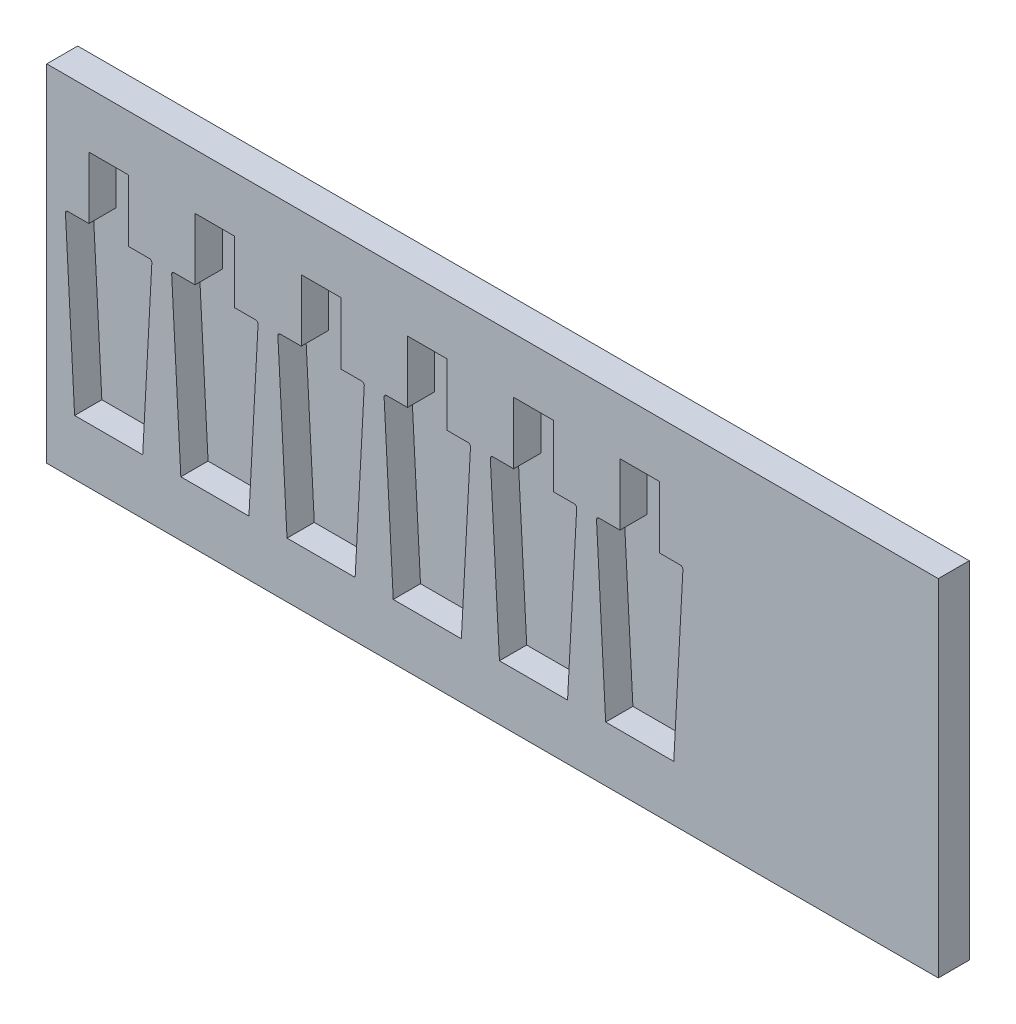
SolidWorks part; units mm, degrees
other "Markup1"
sketch "Sketch5" plane through (-360, -139.665, 25) normal (0, 0, 1) x (1, 0, 0)
ref_plane "Front Plane" through (0, 0, 0) normal (0, 0, 1) x (1, 0, 0)
ref_plane "Top Plane" through (0, 0, 0) normal (0, 1, 0) x (1, 0, 0)
ref_plane "Right Plane" through (0, 0, 0) normal (1, 0, 0) x (0, 0, -1)
sketch "Sketch2" plane through (0, 0, 0) normal (0, 0, 1) x (1, 0, 0)
  line L1 (-360, 139.665) -> (360, 139.665)
  line L2 (-360, 139.665) -> (-360, -139.665)
  line L3 (-360, -139.665) -> (360, -139.665)
  line L4 (360, 139.665) -> (360, -139.665)
  line L5 (-360, 139.665) -> (360, -139.665) construction
  line L6 (-360, -139.665) -> (360, 139.665) construction
  point P0 (0, 0)
  dimension "D1" = 720
  dimension "D2" = 279.33
extrude "Boss-Extrude1" add sketch "Sketch2" along normal blind 25
sketch "Sketch3" plane through (0, 0, 0) normal (0, 0, 1) x (1, 0, 0)
  line L0 (-326, 45) -> (-326, 95)
  line L1 (-326, 95) -> (-294, 95)
  line L2 (-294, 95) -> (-294, 45)
  line L3 (-294, 45) -> (-277.11, 45)
  line L5 (-282.5, -95) -> (-337.5, -95)
  line L7 (-342.89, 45) -> (-326, 45)
  line L9 (-344.8871, 42.893) -> (-337.5, -95)
  line L10 (-275.1129, 42.893) -> (-282.5, -95)
  line L12 (-360, -139.665) -> (360, -139.665) construction
  line L13 (-360, 139.665) -> (-360, -139.665) construction
  line L14 (-189.3386, 42.893) -> (-196.7257, -95)
  line L15 (-196.7257, -95) -> (-251.7257, -95)
  line L16 (-259.1129, 42.893) -> (-251.7257, -95)
  line L17 (-257.1157, 45) -> (-240.2257, 45)
  line L18 (-240.2257, 45) -> (-240.2257, 95)
  line L19 (-240.2257, 95) -> (-208.2257, 95)
  line L20 (-208.2257, 95) -> (-208.2257, 45)
  line L21 (-208.2257, 45) -> (-191.3358, 45)
  line L22 (-103.5644, 42.893) -> (-110.9515, -95)
  line L23 (-110.9515, -95) -> (-165.9515, -95)
  line L24 (-173.3386, 42.893) -> (-165.9515, -95)
  line L25 (-171.3415, 45) -> (-154.4515, 45)
  line L26 (-154.4515, 45) -> (-154.4515, 95)
  line L27 (-154.4515, 95) -> (-122.4515, 95)
  line L28 (-122.4515, 95) -> (-122.4515, 45)
  line L29 (-122.4515, 45) -> (-105.5615, 45)
  line L30 (-17.7901, 42.893) -> (-25.1772, -95)
  line L31 (-25.1772, -95) -> (-80.1772, -95)
  line L32 (-87.5644, 42.893) -> (-80.1772, -95)
  line L33 (-85.5672, 45) -> (-68.6772, 45)
  line L34 (-68.6772, 45) -> (-68.6772, 95)
  line L35 (-68.6772, 95) -> (-36.6772, 95)
  line L36 (-36.6772, 95) -> (-36.6772, 45)
  line L37 (-36.6772, 45) -> (-19.7873, 45)
  line L38 (67.9841, 42.893) -> (60.597, -95)
  line L39 (60.597, -95) -> (5.597, -95)
  line L40 (-1.7901, 42.893) -> (5.597, -95)
  line L41 (0.207, 45) -> (17.097, 45)
  line L42 (17.097, 45) -> (17.097, 95)
  line L43 (17.097, 95) -> (49.097, 95)
  line L44 (49.097, 95) -> (49.097, 45)
  line L45 (49.097, 45) -> (65.987, 45)
  line L46 (153.7584, 42.893) -> (146.3713, -95)
  line L47 (146.3713, -95) -> (91.3713, -95)
  line L48 (83.9841, 42.893) -> (91.3713, -95)
  line L49 (85.9813, 45) -> (102.8713, 45)
  line L50 (102.8713, 45) -> (102.8713, 95)
  line L51 (102.8713, 95) -> (134.8713, 95)
  line L52 (134.8713, 95) -> (134.8713, 45)
  line L53 (134.8713, 45) -> (151.7612, 45)
  arc A0 (-277.11, 45) -> (-275.1129, 42.893) centre (-277.11, 43) cw
  arc A1 (-344.8871, 42.893) -> (-342.89, 45) centre (-342.89, 43) cw
  arc A2 (-191.3358, 45) -> (-189.3386, 42.893) centre (-191.3358, 43) cw
  arc A3 (-259.1129, 42.893) -> (-257.1157, 45) centre (-257.1157, 43) cw
  arc A4 (-105.5615, 45) -> (-103.5644, 42.893) centre (-105.5615, 43) cw
  arc A5 (-173.3386, 42.893) -> (-171.3415, 45) centre (-171.3415, 43) cw
  arc A6 (-19.7873, 45) -> (-17.7901, 42.893) centre (-19.7873, 43) cw
  arc A7 (-87.5644, 42.893) -> (-85.5672, 45) centre (-85.5672, 43) cw
  arc A8 (65.987, 45) -> (67.9841, 42.893) centre (65.987, 43) cw
  arc A9 (-1.7901, 42.893) -> (0.207, 45) centre (0.207, 43) cw
  arc A10 (151.7612, 45) -> (153.7584, 42.893) centre (151.7612, 43) cw
  arc A11 (83.9841, 42.893) -> (85.9813, 45) centre (85.9813, 43) cw
  point P9 (-310, 95)
  point P10 (-310, -95)
  point P16 (-275, 45)
  point P19 (-345, 45)
  dimension "D9" = 2
  dimension "D1" = 50
  dimension "D2" = 190
  dimension "D3" = 70
  dimension "D4" = 32
  dimension "D5" = 55
  dimension "D6" = 19
  dimension "D7" = 44.665
  dimension "D8" = 15
  dimension "D11" = 16
  dimension "D10" = 6
sketch "Sketch4" plane through (0, 0, 25) normal (0, 0, 1) x (1, 0, 0)
  line L8 (-326, 45) -> (-342.89, 45)
  line L9 (-326, 95) -> (-326, 45)
  line L10 (-294, 95) -> (-326, 95)
  line L11 (-294, 45) -> (-294, 95)
  line L12 (-277.11, 45) -> (-294, 45)
  line L13 (-282.5, -95) -> (-275.1129, 42.893)
  line L14 (-337.5, -95) -> (-282.5, -95)
  line L15 (-344.8871, 42.893) -> (-337.5, -95)
  line L16 (-326, 45) -> (-342.89, 45)
  line L17 (-326, 95) -> (-326, 45)
  line L18 (-294, 95) -> (-326, 95)
  line L19 (-294, 45) -> (-294, 95)
  line L20 (-277.11, 45) -> (-294, 45)
  line L21 (-282.5, -95) -> (-275.1129, 42.893)
  line L22 (-337.5, -95) -> (-282.5, -95)
  line L23 (-344.8871, 42.893) -> (-337.5, -95)
  line L24 (-110.9515, -95) -> (-103.5644, 42.893)
  line L25 (-165.9515, -95) -> (-110.9515, -95)
  line L26 (-173.3386, 42.893) -> (-165.9515, -95)
  line L27 (-154.4515, 45) -> (-171.3415, 45)
  line L28 (-154.4515, 95) -> (-154.4515, 45)
  line L29 (-122.4515, 95) -> (-154.4515, 95)
  line L30 (-122.4515, 45) -> (-122.4515, 95)
  line L31 (-105.5615, 45) -> (-122.4515, 45)
  line L32 (-110.9515, -95) -> (-103.5644, 42.893)
  line L33 (-165.9515, -95) -> (-110.9515, -95)
  line L34 (-173.3386, 42.893) -> (-165.9515, -95)
  line L35 (-154.4515, 45) -> (-171.3415, 45)
  line L36 (-154.4515, 95) -> (-154.4515, 45)
  line L37 (-122.4515, 95) -> (-154.4515, 95)
  line L38 (-122.4515, 45) -> (-122.4515, 95)
  line L39 (-105.5615, 45) -> (-122.4515, 45)
  line L40 (-259.1129, 42.893) -> (-251.7257, -95)
  line L41 (-251.7257, -95) -> (-196.7257, -95)
  line L42 (-196.7257, -95) -> (-189.3386, 42.893)
  line L43 (-191.3358, 45) -> (-208.2257, 45)
  line L44 (-208.2257, 45) -> (-208.2257, 95)
  line L45 (-208.2257, 95) -> (-240.2257, 95)
  line L46 (-240.2257, 95) -> (-240.2257, 45)
  line L47 (-240.2257, 45) -> (-257.1157, 45)
  line L48 (-259.1129, 42.893) -> (-251.7257, -95)
  line L49 (-251.7257, -95) -> (-196.7257, -95)
  line L50 (-196.7257, -95) -> (-189.3386, 42.893)
  line L51 (-191.3358, 45) -> (-208.2257, 45)
  line L52 (-208.2257, 45) -> (-208.2257, 95)
  line L53 (-208.2257, 95) -> (-240.2257, 95)
  line L54 (-240.2257, 95) -> (-240.2257, 45)
  line L55 (-240.2257, 45) -> (-257.1157, 45)
  line L56 (-25.1772, -95) -> (-17.7901, 42.893)
  line L57 (-80.1772, -95) -> (-25.1772, -95)
  line L58 (-87.5644, 42.893) -> (-80.1772, -95)
  line L59 (-68.6772, 45) -> (-85.5672, 45)
  line L60 (-68.6772, 95) -> (-68.6772, 45)
  line L61 (-36.6772, 95) -> (-68.6772, 95)
  line L62 (-36.6772, 45) -> (-36.6772, 95)
  line L63 (-19.7873, 45) -> (-36.6772, 45)
  line L64 (-25.1772, -95) -> (-17.7901, 42.893)
  line L65 (-80.1772, -95) -> (-25.1772, -95)
  line L66 (-87.5644, 42.893) -> (-80.1772, -95)
  line L67 (-68.6772, 45) -> (-85.5672, 45)
  line L68 (-68.6772, 95) -> (-68.6772, 45)
  line L69 (-36.6772, 95) -> (-68.6772, 95)
  line L70 (-36.6772, 45) -> (-36.6772, 95)
  line L71 (-19.7873, 45) -> (-36.6772, 45)
  line L72 (60.597, -95) -> (67.9841, 42.893)
  line L73 (5.597, -95) -> (60.597, -95)
  line L74 (-1.7901, 42.893) -> (5.597, -95)
  line L75 (17.097, 45) -> (0.207, 45)
  line L76 (17.097, 95) -> (17.097, 45)
  line L77 (49.097, 95) -> (17.097, 95)
  line L78 (49.097, 45) -> (49.097, 95)
  line L79 (65.987, 45) -> (49.097, 45)
  line L80 (60.597, -95) -> (67.9841, 42.893)
  line L81 (5.597, -95) -> (60.597, -95)
  line L82 (-1.7901, 42.893) -> (5.597, -95)
  line L83 (17.097, 45) -> (0.207, 45)
  line L84 (17.097, 95) -> (17.097, 45)
  line L85 (49.097, 95) -> (17.097, 95)
  line L86 (49.097, 45) -> (49.097, 95)
  line L87 (65.987, 45) -> (49.097, 45)
  line L88 (83.9841, 42.893) -> (91.3713, -95)
  line L89 (91.3713, -95) -> (146.3713, -95)
  line L90 (146.3713, -95) -> (153.7584, 42.893)
  line L91 (151.7612, 45) -> (134.8713, 45)
  line L92 (134.8713, 45) -> (134.8713, 95)
  line L93 (134.8713, 95) -> (102.8713, 95)
  line L94 (102.8713, 95) -> (102.8713, 45)
  line L95 (102.8713, 45) -> (85.9813, 45)
  line L96 (83.9841, 42.893) -> (91.3713, -95)
  line L97 (91.3713, -95) -> (146.3713, -95)
  line L98 (146.3713, -95) -> (153.7584, 42.893)
  line L99 (151.7612, 45) -> (134.8713, 45)
  line L100 (134.8713, 45) -> (134.8713, 95)
  line L101 (134.8713, 95) -> (102.8713, 95)
  line L102 (102.8713, 95) -> (102.8713, 45)
  line L103 (102.8713, 45) -> (85.9813, 45)
  arc A2 (-275.1129, 42.893) -> (-277.11, 45) centre (-277.11, 43) ccw
  arc A3 (-342.89, 45) -> (-344.8871, 42.893) centre (-342.89, 43) ccw
  arc A4 (-275.1129, 42.893) -> (-277.11, 45) centre (-277.11, 43) ccw
  arc A5 (-342.89, 45) -> (-344.8871, 42.893) centre (-342.89, 43) ccw
  arc A6 (-171.3415, 45) -> (-173.3386, 42.893) centre (-171.3415, 43) ccw
  arc A7 (-103.5644, 42.893) -> (-105.5615, 45) centre (-105.5615, 43) ccw
  arc A8 (-171.3415, 45) -> (-173.3386, 42.893) centre (-171.3415, 43) ccw
  arc A9 (-103.5644, 42.893) -> (-105.5615, 45) centre (-105.5615, 43) ccw
  arc A10 (-257.1157, 45) -> (-259.1129, 42.893) centre (-257.1157, 43) ccw
  arc A11 (-189.3386, 42.893) -> (-191.3358, 45) centre (-191.3358, 43) ccw
  arc A12 (-257.1157, 45) -> (-259.1129, 42.893) centre (-257.1157, 43) ccw
  arc A13 (-189.3386, 42.893) -> (-191.3358, 45) centre (-191.3358, 43) ccw
  arc A14 (-85.5672, 45) -> (-87.5644, 42.893) centre (-85.5672, 43) ccw
  arc A15 (-17.7901, 42.893) -> (-19.7873, 45) centre (-19.7873, 43) ccw
  arc A16 (-85.5672, 45) -> (-87.5644, 42.893) centre (-85.5672, 43) ccw
  arc A17 (-17.7901, 42.893) -> (-19.7873, 45) centre (-19.7873, 43) ccw
  arc A18 (0.207, 45) -> (-1.7901, 42.893) centre (0.207, 43) ccw
  arc A19 (67.9841, 42.893) -> (65.987, 45) centre (65.987, 43) ccw
  arc A20 (0.207, 45) -> (-1.7901, 42.893) centre (0.207, 43) ccw
  arc A21 (67.9841, 42.893) -> (65.987, 45) centre (65.987, 43) ccw
  arc A22 (85.9813, 45) -> (83.9841, 42.893) centre (85.9813, 43) ccw
  arc A23 (153.7584, 42.893) -> (151.7612, 45) centre (151.7612, 43) ccw
  arc A24 (85.9813, 45) -> (83.9841, 42.893) centre (85.9813, 43) ccw
  arc A25 (153.7584, 42.893) -> (151.7612, 45) centre (151.7612, 43) ccw
  dimension "D1" = 0
  dimension "D2" = 0
  dimension "D3" = 0
  dimension "D4" = 0
  dimension "D5" = 0
  dimension "D6" = 0
extrude "Cut-Extrude1" cut sketch "Sketch4" against normal offset from surface (22 mm away) 3 up to face at (0, 0, 0)
